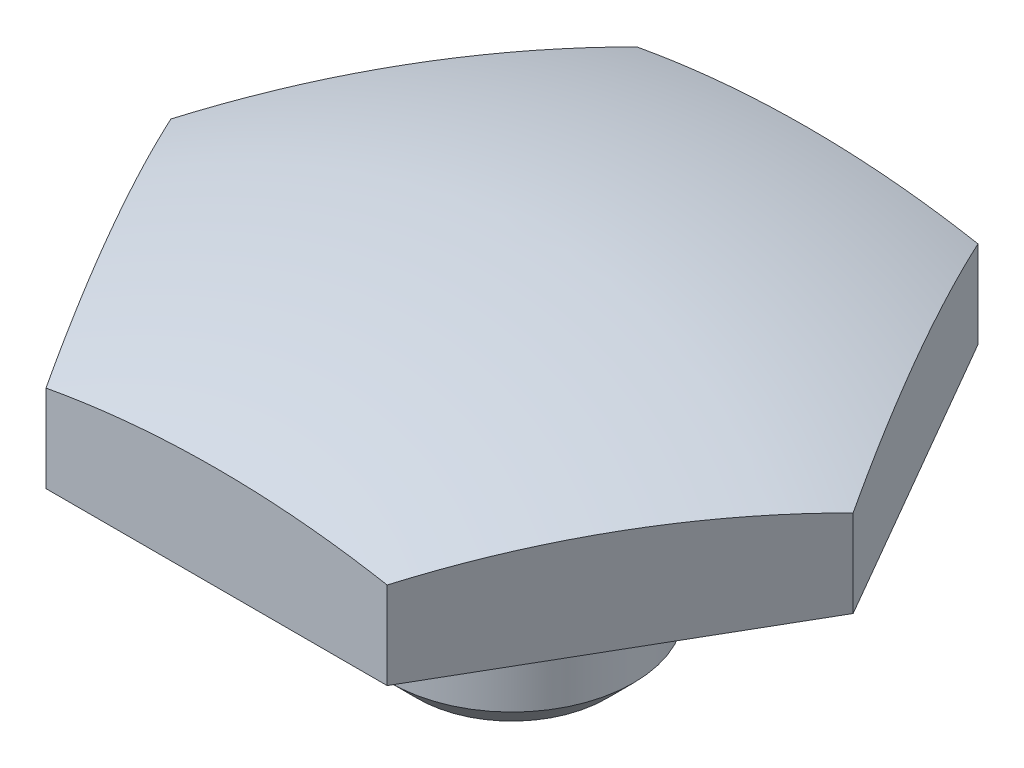
SolidWorks part; units mm, degrees
ref_plane "Front Plane" through (0, 0, 0) normal (0, 0, 1) x (1, 0, 0)
ref_plane "Top Plane" through (0, 0, 0) normal (0, 1, 0) x (1, 0, 0)
ref_plane "Right Plane" through (0, 0, 0) normal (1, 0, 0) x (0, 0, -1)
sketch "Sketch3" plane through (0, 0, 0) normal (0, 0, 1) x (1, 0, 0)
  line L1 (3.9116, 3.5052) -> (3.9116, 0.8636)
  line L2 (10.9985, 6.35) -> (3.429, 6.35)
  line L3 (3.048, 5.969) -> (3.048, 4.3688)
  line L4 (3.048, 4.3688) -> (3.9116, 3.5052)
  line L5 (0, 11.1252) -> (0, 0)
  line L6 (3.9116, 0.8636) -> (3.048, 0)
  line L7 (10.9985, 9.1593) -> (10.9985, 6.35)
  line L8 (0, 0) -> (3.048, 0)
  line L10 (0, -1000) -> (0, 49000) construction
  arc A0 (3.429, 6.35) -> (3.048, 5.969) centre (3.429, 5.969) ccw
  arc A1 (10.9985, 9.1593) -> (0, 11.1252) centre (0, -20.6248) ccw
  dimension "D10" = 0.381
  dimension "D3" = 63.5
  dimension "D1" = 1.9812
  dimension "D2" = 6.35
  dimension "D4" = 21.997
  dimension "D5" = 45
  dimension "D6" = 45
  dimension "D7" = 7.8232
  dimension "D8" = 6.096
  dimension "D9" = 11.1252
revolve "Revolve1" add sketch "Sketch3" angle 360 about L10
cosmetic thread "5/16-24 UNF" parameters "D2"=7.1628
sketch "Sketch1" plane through (0, 0, 0) normal (0, 1, 0) x (1, 0, 0)
  line L1 (10.9985, 0) -> (5.4993, 9.525)
  line L2 (5.4993, 9.525) -> (-5.4993, 9.525)
  line L3 (-5.4993, 9.525) -> (-10.9985, 0)
  line L4 (-10.9985, 0) -> (-5.4993, -9.525)
  line L5 (-5.4993, -9.525) -> (5.4993, -9.525)
  line L6 (5.4993, -9.525) -> (10.9985, 0)
  circle A0 centre (0, 0) radius 9.525 construction
  circle A1 centre (0, 0) radius 10.9985
  dimension "D1" = 19.05
extrude "Cut-Extrude2" cut sketch "Sketch1" along normal blind 11.1252 contours L5 A1 | L4 A1 | L6 A1 | L1 A1 | L2 A1 | L3 A1
